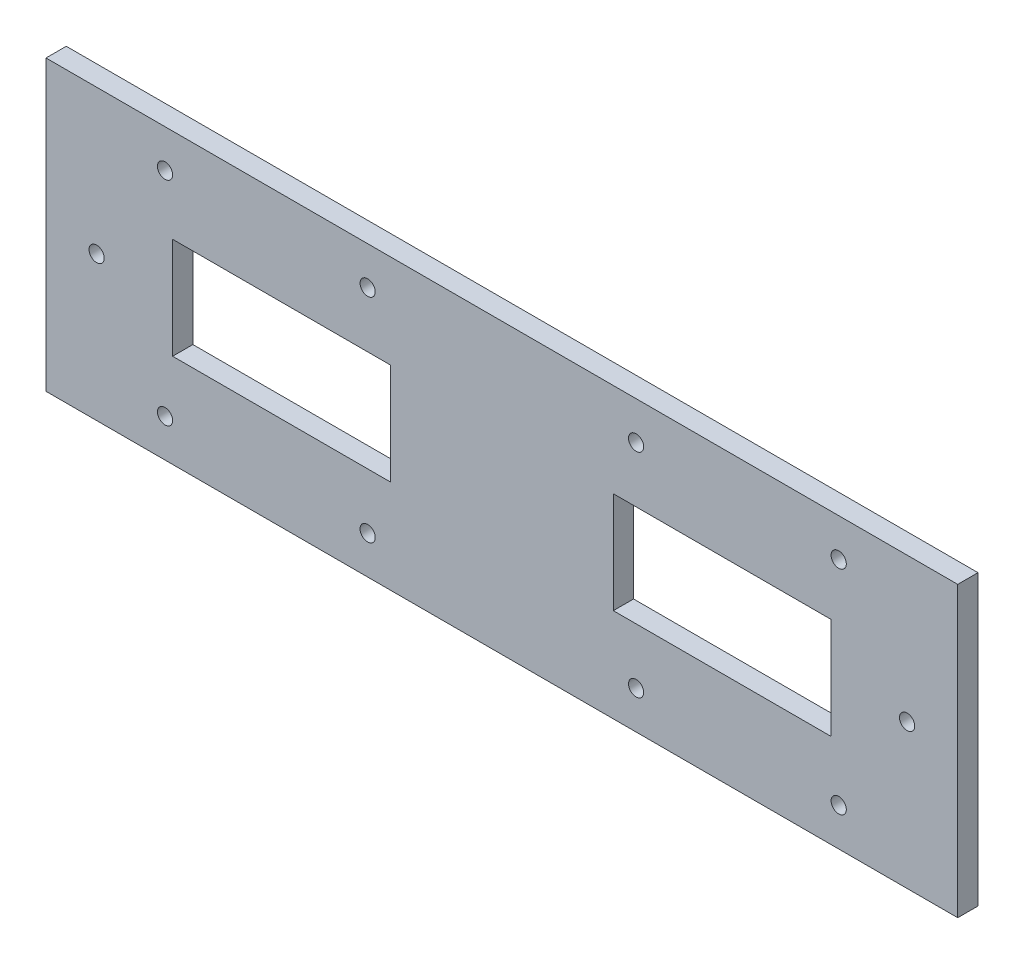
SolidWorks part; units mm, degrees
ref_plane "Front Plane" through (0, 0, 0) normal (0, 0, 1) x (1, 0, 0)
ref_plane "Top Plane" through (0, 0, 0) normal (0, 1, 0) x (1, 0, 0)
ref_plane "Right Plane" through (0, 0, 0) normal (1, 0, 0) x (0, 0, -1)
sketch "Sketch1" plane through (0, 0, 0) normal (0, 0, 1) x (1, 0, 0)
  line L0 (40.4436, 7.2233) -> (83.4436, 7.2233)
  line L1 (-71.5564, 25.7233) -> (108.4436, 25.7233)
  line L2 (-71.5564, 25.7233) -> (-71.5564, -31.2767)
  line L3 (-71.5564, -31.2767) -> (108.4436, -31.2767)
  line L4 (108.4436, 25.7233) -> (108.4436, -31.2767)
  line L5 (40.4436, -12.7767) -> (83.4436, -12.7767)
  line L6 (-46.5564, 7.2233) -> (-3.5564, 7.2233)
  line L7 (-46.5564, 7.2233) -> (-46.5564, -12.7767)
  line L8 (-46.5564, -12.7767) -> (-3.5564, -12.7767)
  line L9 (83.4436, 7.2233) -> (83.4436, -12.7767)
  line L10 (28.4436, 25.7233) -> (8.4436, 25.7233)
  line L11 (40.4436, 7.2233) -> (40.4436, -12.7767)
  line L12 (28.4436, -31.2767) -> (8.4436, -31.2767)
  line L13 (-3.5564, 7.2233) -> (-3.5564, -12.7767)
  circle A0 centre (-48.0564, 18.2233) radius 1.5
  circle A1 centre (-8.0564, 18.2233) radius 1.5
  circle A2 centre (44.9436, 18.2233) radius 1.5
  circle A3 centre (84.9436, 18.2233) radius 1.5
  circle A4 centre (44.9436, -23.7767) radius 1.5
  circle A5 centre (84.9436, -23.7767) radius 1.5
  circle A6 centre (-48.0564, -23.7767) radius 1.5
  circle A7 centre (-8.0564, -23.7767) radius 1.5
  circle A8 centre (-61.5564, -2.7767) radius 1.5
  circle A9 centre (98.4436, -2.7767) radius 1.5
  dimension "D5" = 40
  dimension "D6" = 23.5
  dimension "D12" = 10
  dimension "D13" = 10
  dimension "D1" = 18.5
  dimension "D2" = 18.5
  dimension "D3" = 25
  dimension "D4" = 25
  dimension "D7" = 57
  dimension "D8" = 7.5
  dimension "D11" = 180
  dimension "D14" = 28.5
  dimension "D9" = 2
  dimension "D10" = 2
extrude "Boss-Extrude3" add sketch "Sketch1" against normal blind 4 contours L4 L1 L2 L3 A7 A6 A5 A4 A3 A2 A1 A0 L11 L0 L9 L5 L6 L13 L8 L7
